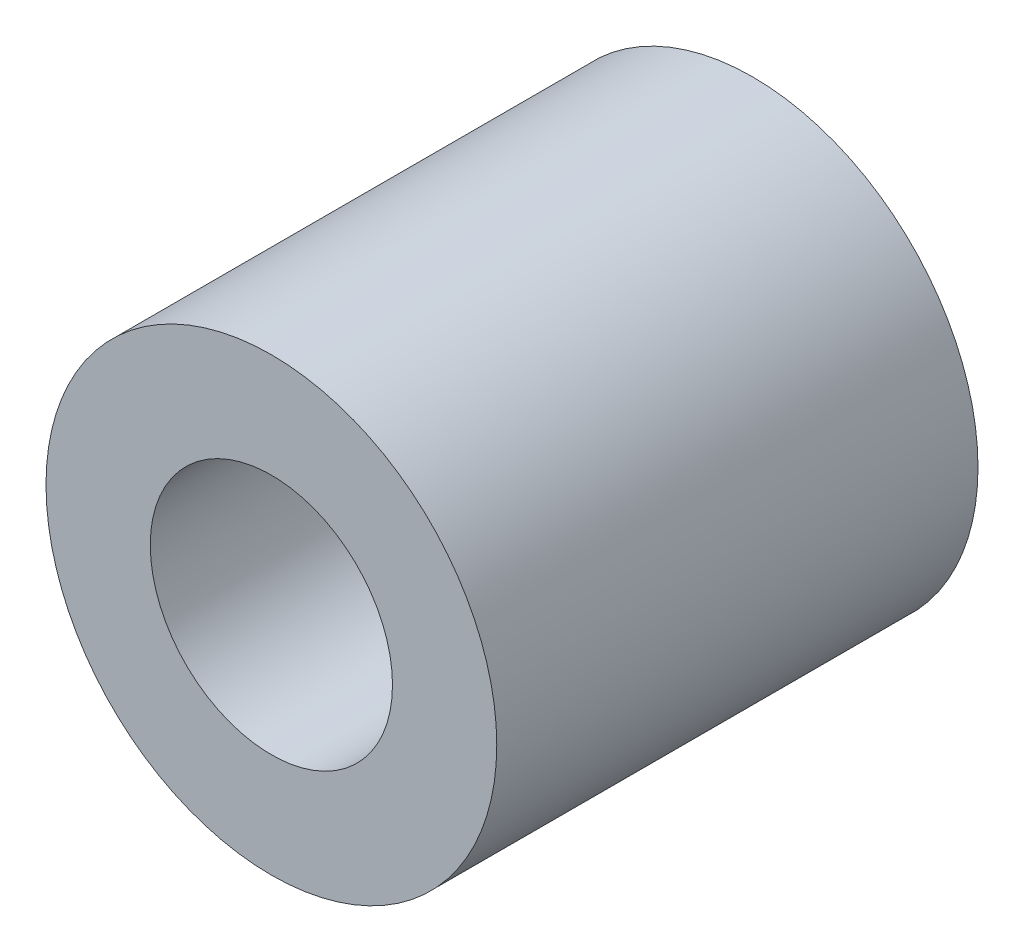
SolidWorks part; units mm, degrees
ref_plane "Front Plane" through (0, 0, 0) normal (0, 0, 1) x (1, 0, 0)
ref_plane "Top Plane" through (0, 0, 0) normal (0, 1, 0) x (1, 0, 0)
ref_plane "Right Plane" through (0, 0, 0) normal (1, 0, 0) x (0, 0, -1)
sketch "Sketch1" plane through (0, 0, 0) normal (0, 0, 1) x (1, 0, 0)
  circle A0 centre (0, 0) radius 0.755 construction
  circle A1 centre (0, 0) radius 1.405
  dimension "D1" = 1.51
  dimension "D2" = 0.65
extrude "Boss-Extrude1" add sketch "Sketch1" along normal blind 3
sketch "Sketch2" plane through (0, 0, 3) normal (0, 0, 1) x (1, 0, 0)
  circle A0 centre (0, 0) radius 0.755
  circle A1 centre (0, 0) radius 1.405
  circle A2 centre (0, 0) radius 1.405 construction
  dimension "D2" = 1.51
  dimension "D1" = 0
extrude "Cut-Extrude1" cut sketch "Sketch2" against normal blind 2.8
